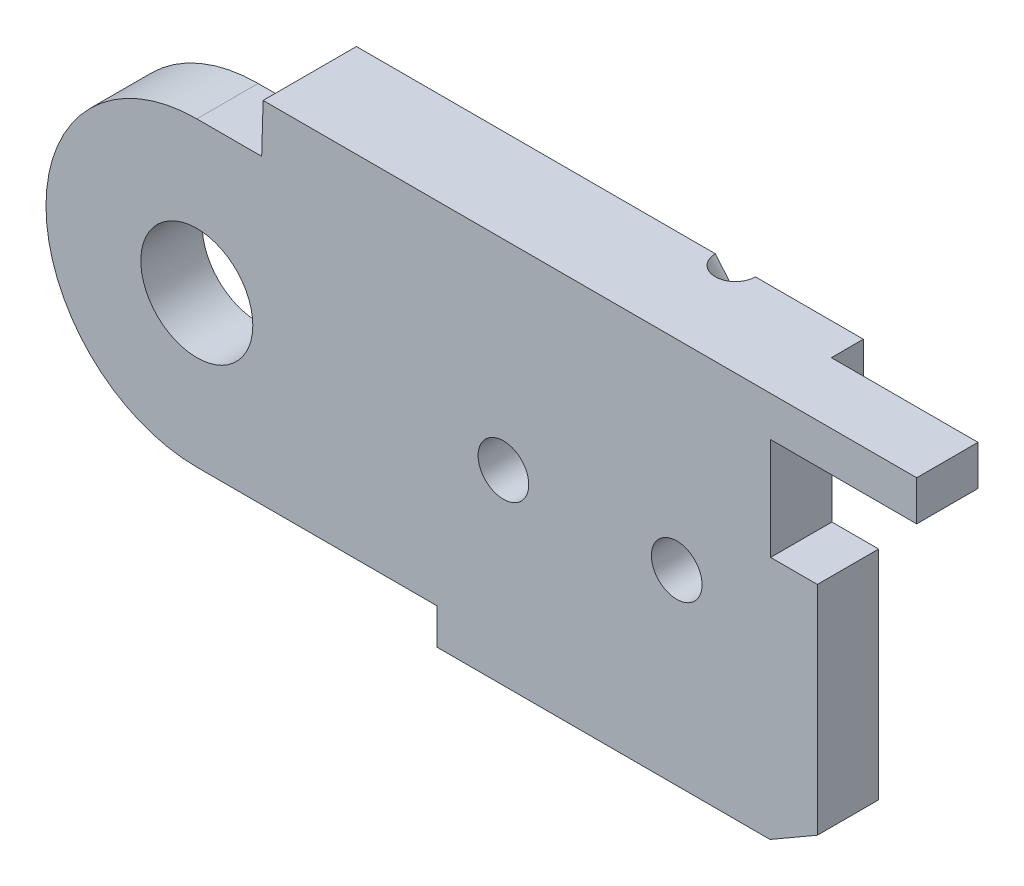
SolidWorks part; units mm, degrees
ref_plane "Front Plane" through (0, 0, 0) normal (0, 0, 1) x (1, 0, 0)
ref_plane "Top Plane" through (0, 0, 0) normal (0, 1, 0) x (1, 0, 0)
ref_plane "Right Plane" through (0, 0, 0) normal (1, 0, 0) x (0, 0, -1)
sketch "Sketch3" plane through (0, 0, 0) normal (0, 0, 1) x (1, 0, 0)
  line L7 (8, 0) -> (9, -2.5)
  line L11 (30, 7) -> (27, 7.5)
  line L13 (0, 7) -> (0, 7.5) construction
  line L14 (0, 7.5) -> (-22.3287, 7.5) construction
  line L15 (0, 5.3) -> (-14, 5.3) construction
  line L16 (0, 4) -> (-14, 4) construction
  line L17 (-14, 4) -> (-14, 5.3) construction
  line L18 (5.6569, 5.6569) -> (5.6569, 7.5)
  line L19 (5.6569, 7.5) -> (27, 7.5)
  line L20 (21.5, -7) -> (9, -7)
  line L21 (9, -7) -> (9, -2.5)
  line L23 (25.0503, -4.9497) -> (21.5, -7)
  arc A4 (8, 0) -> (5.6569, 5.6569) centre (0, 0) ccw
  arc A5 (25.0503, -4.9497) -> (30, 7) centre (30, 0) ccw
  circle A6 centre (0, 0) radius 7 construction
  circle A7 centre (0, 0) radius 3.9 construction
  circle A8 centre (0, 0) radius 5.3 construction
  circle A9 centre (0, 0) radius 4 construction
  dimension "D10" = 0.5
  dimension "D17" = 14
  dimension "D5" = 135
  dimension "D6" = 12.5
  dimension "D7" = 4.5
  dimension "D8" = 1
  dimension "D9" = 45
  dimension "D11" = 1.8431
  dimension "D12" = 30
  dimension "D14" = 3
extrude "Boss-Extrude1" add sketch "Sketch3" along normal blind 2 contours A5 L11 L19 L18 A4 L7 L21 L20 L23
sketch "Sketch20" plane through (0, 0, 0) normal (0, 0, 1) x (1, 0, 0)
  line L0 (0, 7) -> (0, 7.5) construction
  line L1 (0, 7.5) -> (-19.4737, 7.5) construction
  line L2 (0, 5.3) -> (-14, 5.3) construction
  line L3 (0, 4) -> (-14, 4) construction
  line L4 (-14, 4) -> (-14, 5.3) construction
  line L5 (0, 5.3) -> (17.4849, 5.3) construction
  line L6 (17.4849, 5.3) -> (17.4849, 4) construction
  line L7 (17.4849, 4) -> (0, 4) construction
  line L8 (-2.5, 7.5) -> (-2.5, 2.868) construction
  circle A0 centre (0, 0) radius 7 construction
  circle A1 centre (0, 0) radius 3.9 construction
  circle A3 centre (0, 0) radius 5.3 construction
  circle A4 centre (0, 0) radius 4 construction
  circle A5 centre (0, 0) radius 2 construction
  dimension "D1" = 0
  dimension "D2" = 2.5
ref_plane "Plane1" through (0, 0, 2) normal (0, 0, 1) x (1, 0, 0)
sketch "Sketch4" plane through (0, 0, 2) normal (0, 0, 1) x (1, 0, 0)
  line L4 (5.6569, 5.6569) -> (5.6569, 7.5)
  line L5 (5.6569, 5.6569) -> (5.6569, 7.5) construction
  line L6 (5.6569, 7.5) -> (21.5, 7.5)
  line L10 (8, 0) -> (9, -2.5)
  line L11 (9, -2.5) -> (9, -7)
  line L12 (9, -7) -> (21.5, -7)
  line L13 (21.5, -7) -> (21.5, 7.5)
  arc A0 (8, 0) -> (5.6569, 5.6569) centre (0, 0) ccw construction
  arc A3 (8, 0) -> (5.6569, 5.6569) centre (0, 0) ccw
sketch "Sketch22" plane through (0, 0, 2) normal (0, 0, 1) x (1, 0, 0)
  line L0 (5.6569, 5.6569) -> (2.4868, 5.6569)
  line L1 (5.6569, 7.5) -> (21.5, 7.5)
  line L2 (5.6569, 7.5) -> (2.4868, 7.5)
  line L3 (2.4868, 7.5) -> (2.4868, 5.6569)
  line L6 (8, 0) -> (9, -2.5)
  line L7 (9, -2.5) -> (9, -7)
  line L8 (9, -7) -> (21.5, -7)
  line L10 (21.5, 7.5) -> (27, 7.5)
  line L11 (27, 7.5) -> (27, 2.172)
  line L12 (27, 2.172) -> (23.2751, 2.172)
  line L13 (21.5, -7) -> (23.2751, -5.9749)
  line L14 (25.0503, -4.9497) -> (21.5, -7) construction
  line L15 (23.2751, -5.9749) -> (23.2751, 2.172)
  arc A0 (8, 0) -> (5.6569, 5.6569) centre (0, 0) ccw
extrude "Boss-Extrude6" add sketch "Sketch22" along normal blind 2.5
sketch "Sketch25" plane through (0, 0, 2) normal (0, 0, 1) x (1, 0, 0)
  line L0 (0, 5.3) -> (18.0981, 5.3) construction
  line L1 (0, 4) -> (18.0981, 4) construction
  line L2 (18.0981, 4) -> (18.0981, 5.3) construction
sketch "Sketch26" plane through (0, 0, 2) normal (0, 0, 1) x (1, 0, 0)
  line L1 (18.0981, 5.3) -> (2.5301, 5.3)
  line L2 (18.0981, 4) -> (2.5301, 4)
  line L3 (2.5301, 5.3) -> (2.5301, 4)
  line L4 (18.0981, 5.3) -> (27, 5.3)
  line L5 (27, 2.172) -> (27, 7.5) construction
  line L6 (27, 5.3) -> (27, 4)
  line L7 (27, 4) -> (18.0981, 4)
extrude "Cut-Extrude6" cut sketch "Sketch26" along normal blind 2.5
ref_plane "Plane18" through (0, 0, 4.5) normal (0, 0, 1) x (1, 0, 0)
sketch "Sketch31" plane through (0, 0, 4.5) normal (0, 0, 1) x (1, 0, 0)
  line L0 (2.4327, 5.6569) -> (0, 5.6569)
  line L4 (9, -5.6569) -> (0, -5.6569)
  line L5 (2.4327, 5.6569) -> (2.4868, 7.5)
  line L12 (9, -7) -> (9, -5.6569)
  line L13 (9, -2.5) -> (9, -7) construction
  line L16 (27, 7.5) -> (27, 2.172)
  line L17 (27, 2.172) -> (23.2751, 2.172)
  line L18 (23.2751, -5.9749) -> (23.2751, 2.172)
  line L19 (27, 7.5) -> (2.4868, 7.5)
  line L20 (9, -7) -> (21.5, -7)
  line L21 (21.5, -7) -> (23.2751, -5.9749)
  arc A0 (0, 5.6569) -> (0, -5.6569) centre (0, 0) ccw
  dimension "D1" = 5.6569
extrude "Boss-Extrude14" add sketch "Sketch31" along normal blind 2.3 separate body
sketch "Sketch32" plane through (0, 0, 6.8) normal (0, 0, 1) x (1, 0, 0)
  circle A0 centre (0, 0) radius 2.1
extrude "Cut-Extrude7" cut sketch "Sketch32" against normal blind 2.3
sketch "Sketch33" plane through (0, 0, 6.8) normal (0, 0, 1) x (1, 0, 0)
  line L4 (9, -5.6569) -> (9, -7)
  line L11 (9, -7) -> (21.5, -7)
  line L15 (21.5, -7) -> (21.5, -5.6569)
  line L16 (21.5, -5.6569) -> (9, -5.6569)
  line L17 (2.4868, 7.5) -> (21.5, 7.5)
  line L18 (27, 7.5) -> (2.4868, 7.5) construction
  line L19 (2.4868, 7.5) -> (2.4327, 5.6569)
  line L20 (2.4327, 5.6569) -> (21.5, 5.6569)
  line L21 (21.5, 5.6569) -> (21.5, 7.5)
extrude "Boss-Extrude15" add sketch "Sketch33" along normal blind 1.2
sketch "Sketch34" plane through (0, 0, 2) normal (0, 0, 1) x (1, 0, 0)
  line L0 (30, 5.3) -> (18.0981, 5.3) construction
  line L1 (30, 4) -> (18.0981, 4) construction
  circle A0 centre (30, 0) radius 2 construction
  circle A1 centre (30, 0) radius 5.3 construction
  circle A2 centre (30, 0) radius 4 construction
sketch "Sketch35" plane through (0, 0, 6.8) normal (0, 0, 1) x (1, 0, 0)
  line L0 (27, 2.172) -> (27, 6)
  line L1 (27, 2.172) -> (21.5204, 2.172)
  line L2 (27, 6) -> (21.5204, 6)
  line L3 (21.5204, 2.172) -> (21.5204, 6)
  line L4 (27, 2.172) -> (27, 7.5) construction
extrude "Cut-Extrude8" cut sketch "Sketch35" against normal blind 2.4
sketch "Sketch36" plane through (0, 0, 4.4) normal (0, 0, 1) x (1, 0, 0)
  line L0 (27, 2.172) -> (27, 4)
  line L1 (27, 2.172) -> (23.3, 2.172)
  line L2 (27, 4) -> (23.3, 4)
  line L3 (23.3, 2.172) -> (23.3, 4)
  line L4 (21.5, -7) -> (21.5, 7.5) construction
  dimension "D1" = 1.8
extrude "Cut-Extrude9" cut sketch "Sketch36" against normal blind 2.4
sketch "Sketch37" plane through (0, 0, 2) normal (0, 0, 1) x (1, 0, 0)
  circle A0 centre (30, 0) radius 3.9
extrude "Boss-Extrude16" add sketch "Sketch37" along normal blind 2.3
sketch "Sketch39" plane through (0, 0, 4.3) normal (0, 0, 1) x (1, 0, 0)
  line L0 (29, 1.7321) -> (29, -1.7321)
  arc A0 (29, -1.7321) -> (29, 1.7321) centre (30, 0) ccw
  dimension "D2" = 4
  dimension "D1" = 1
extrude "Cut-Extrude10" cut sketch "Sketch39" against normal through all
sketch "Sketch43" plane through (0, 0, 6.8) normal (0, 0, 1) x (1, 0, 0)
  line L2 (0, -5.6569) -> (9, -5.6569) construction
  circle A0 centre (11.5, 0) radius 2.5
  circle A1 centre (18, 0) radius 2.5
  dimension "D1" = 2.5
  dimension "D3" = 5
  dimension "D4" = 6.5
  dimension "D2" = 5.6569
extrude "Boss-Extrude17" add sketch "Sketch43" along normal blind 1.2
sketch "Sketch44" plane through (0, 0, 8) normal (0, 0, 1) x (1, 0, 0)
  circle A0 centre (11.5, 0) radius 0.95
  circle A1 centre (18, 0) radius 0.95
  dimension "D1" = 1.9
  dimension "D2" = 1.9
extrude "Cut-Extrude11" cut sketch "Sketch44" against normal through all
sketch "Sketch45" plane through (0, 0, 0) normal (0, 0, -1) x (-1, 0, 0)
  circle A0 centre (-11.5, 0) radius 2
  circle A1 centre (-18, 0) radius 2
extrude "Cut-Extrude12" cut sketch "Sketch45" against normal blind 2.5
ref_plane "Plane17" through (0, 0, 8) normal (0, 0, 1) x (1, 0, 0)
sketch "Sketch48" plane through (0, 0, 2) normal (0, 0, 1) x (1, 0, 0)
  circle A0 centre (30, 0) radius 5 construction
sketch "Sketch51" plane through (0, 0, 8) normal (0, 0, 1) x (1, 0, 0)
  line L0 (18.2355, 5.6569) -> (27.0112, -4.8677) construction
  line L1 (2.4327, 5.6569) -> (21.5, 5.6569) construction
sketch "Sketch52" plane through (0, 5.6569, 0) normal (0, -1, 0) x (1, 0, 0)
  circle A0 centre (18.2355, 8) radius 0.75
extrude "Cut-Extrude13" cut sketch "Sketch52" along direction (0.6404, -0.768, 0) on the side against the normal blind 10
mirror "Mirror1" about plane through (0, 0, 8) normal (0, 0, 1) of bodies 133 129
split "Split1" trim tools "Plane17" bodies to split 135 134 resulting bodies 136 137
delete or keep bodies "Body-Delete/Keep 1" type delete bodies bodies 129 133 136
